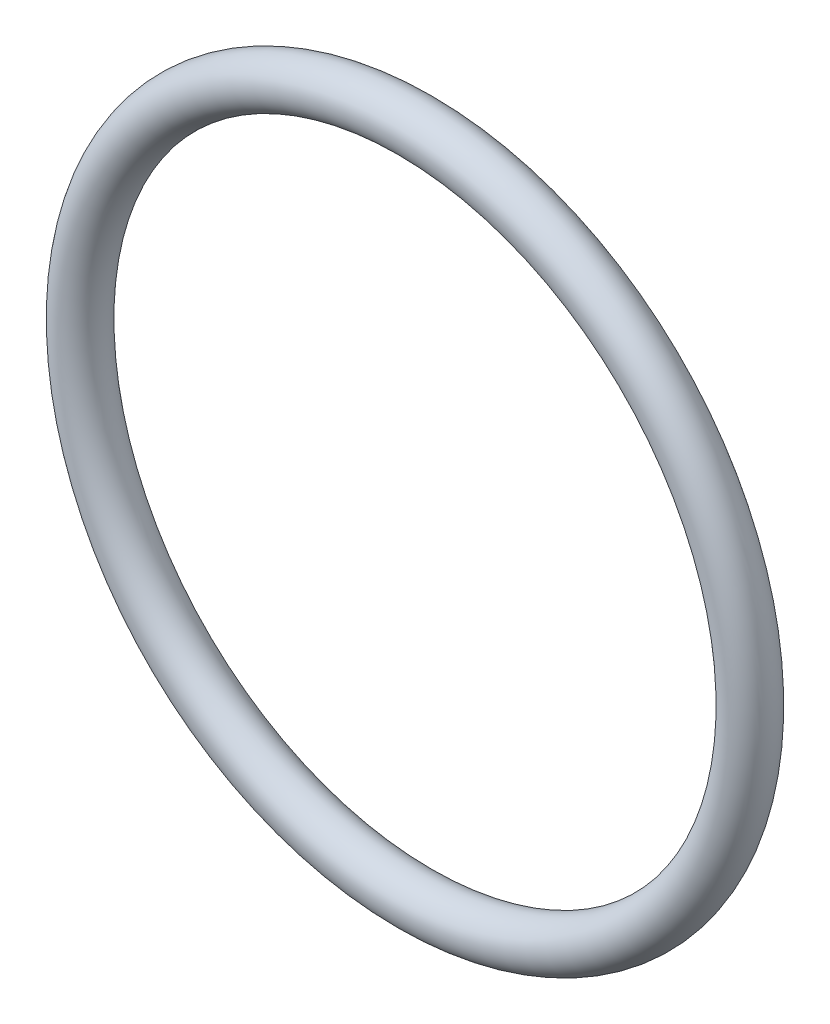
SolidWorks part; units mm, degrees
ref_plane "Plan de face" through (0, 0, 0) normal (0, 0, 1) x (1, 0, 0)
ref_plane "Plan de dessus" through (0, 0, 0) normal (0, 1, 0) x (1, 0, 0)
ref_plane "Plan de droite" through (0, 0, 0) normal (1, 0, 0) x (0, 0, -1)
sketch "Esquisse1" plane through (0, 0, 0) normal (0, 0, 1) x (1, 0, 0)
  line L0 (0, 28) -> (0, 31) construction
  circle A0 centre (0, 0) radius 28
sketch "Esquisse3" plane through (0, 0, 0) normal (1, 0, 0) x (0, 0, -1)
  line L1 (0, 28) -> (0, 31) construction
  line L2 (0, 28) -> (0, -28) construction
  line L3 (0, 0) -> (0, 28) construction
  line L4 (0, 0) -> (0, -28) construction
  circle A1 centre (0, 28) radius 2
  circle A2 centre (0, -28) radius 2 construction
sweep "Balayage5" add profiles "Esquisse3" path "Esquisse1"
